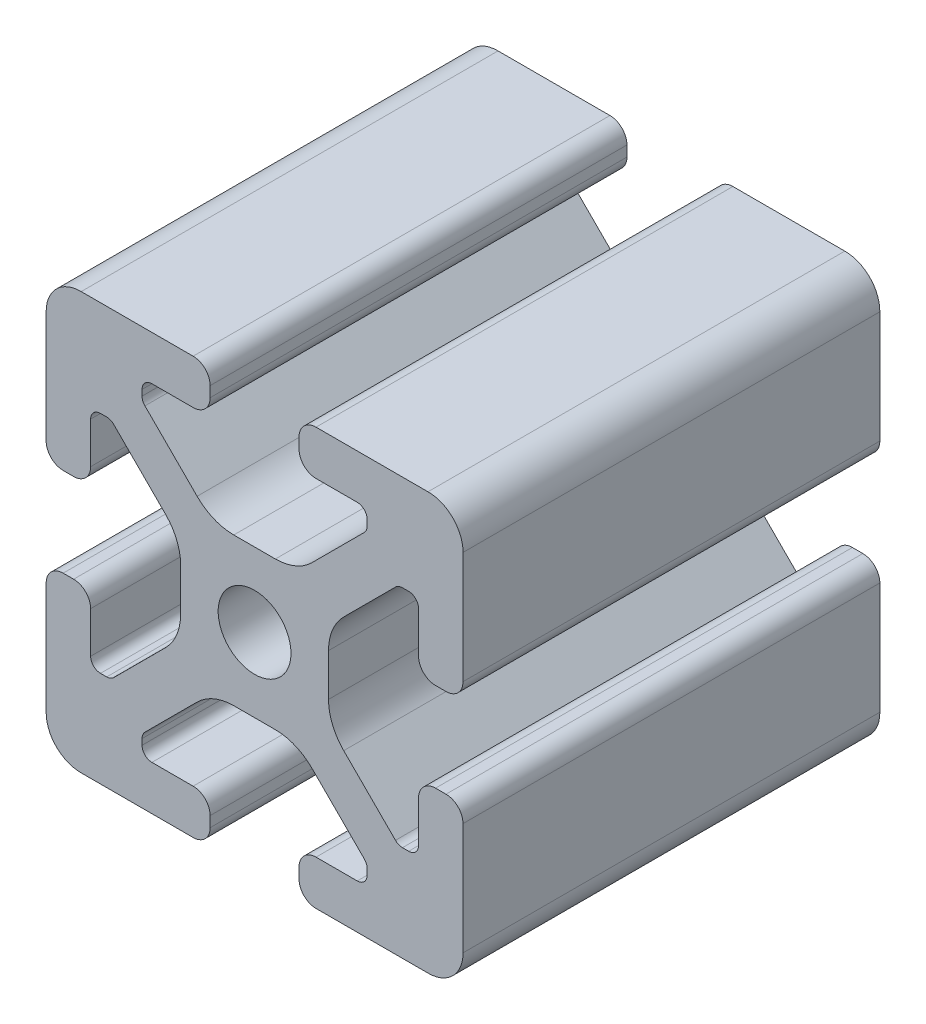
SolidWorks part; units mm, degrees
ref_plane "Front Plane" through (0, 0, 0) normal (0, 0, 1) x (1, 0, 0)
ref_plane "Top Plane" through (0, 0, 0) normal (0, 1, 0) x (1, 0, 0)
ref_plane "Right Plane" through (0, 0, 0) normal (1, 0, 0) x (0, 0, -1)
sketch "Sketch1" plane through (0, 0, 0) normal (0, 0, 1) x (1, 0, 0)
  point P0 (0, 0)
  line B0 (-4.064, 16.5396) -> (-4.064, 17.4964)
  line B1 (-5.6176, 19.05) -> (-15.8475, 19.05)
  line B2 (-19.05, 15.8475) -> (-19.05, 5.6176)
  line B3 (-17.4964, 4.064) -> (-16.5396, 4.064)
  line B4 (-14.986, 5.6176) -> (-14.986, 9.3853)
  line B5 (-14.0843, 10.287) -> (-13.516, 10.287)
  line B6 (-12.8784, 10.0229) -> (-8.1476, 5.2921)
  line B7 (-6.7564, 1.9335) -> (-6.7564, -1.9335)
  line B8 (-8.1476, -5.2921) -> (-12.8784, -10.0229)
  line B9 (-13.516, -10.287) -> (-14.0843, -10.287)
  line B10 (-14.986, -9.3853) -> (-14.986, -5.6176)
  line B11 (-16.5396, -4.064) -> (-17.4964, -4.064)
  line B12 (-19.05, -5.6176) -> (-19.05, -15.8475)
  line B13 (-15.8475, -19.05) -> (-5.6176, -19.05)
  line B14 (-4.064, -17.4964) -> (-4.064, -16.5396)
  line B15 (-5.6176, -14.986) -> (-9.3853, -14.986)
  line B16 (-10.287, -14.0843) -> (-10.287, -13.5524)
  line B17 (-10.0229, -12.9148) -> (-5.2522, -8.144)
  line B18 (-1.9022, -6.7564) -> (1.9022, -6.7564)
  line B19 (5.2522, -8.144) -> (10.0229, -12.9148)
  line B20 (10.287, -13.5524) -> (10.287, -14.0843)
  line B21 (9.3853, -14.986) -> (5.6176, -14.986)
  line B22 (4.064, -16.5396) -> (4.064, -17.4964)
  line B23 (5.6176, -19.05) -> (15.8475, -19.05)
  line B24 (19.05, -15.8475) -> (19.05, -5.6176)
  line B25 (17.4964, -4.064) -> (16.5396, -4.064)
  line B26 (14.986, -5.6176) -> (14.986, -9.3853)
  line B27 (14.0843, -10.287) -> (13.516, -10.287)
  line B28 (12.8784, -10.0229) -> (8.1476, -5.2921)
  line B29 (6.7564, -1.9335) -> (6.7564, 1.9335)
  line B30 (8.1476, 5.2921) -> (12.8784, 10.0229)
  line B31 (13.516, 10.287) -> (14.0843, 10.287)
  line B32 (14.986, 9.3853) -> (14.986, 5.6176)
  line B33 (16.5396, 4.064) -> (17.4964, 4.064)
  line B34 (19.05, 5.6176) -> (19.05, 15.8475)
  line B35 (15.8475, 19.05) -> (5.6176, 19.05)
  line B36 (4.064, 17.4964) -> (4.064, 16.5396)
  line B37 (5.6176, 14.986) -> (9.3853, 14.986)
  line B38 (10.287, 14.0843) -> (10.287, 13.5524)
  line B39 (10.0229, 12.9148) -> (5.2522, 8.144)
  line B40 (1.9022, 6.7564) -> (-1.9022, 6.7564)
  line B41 (-5.2522, 8.144) -> (-10.0229, 12.9148)
  line B42 (-10.287, 13.5524) -> (-10.287, 14.0843)
  line B43 (-9.3853, 14.986) -> (-5.6176, 14.986)
  arc B44 (-5.6176, 14.986) -> (-4.064, 16.5396) centre (-5.6176, 16.5396) ccw
  arc B45 (-4.064, 17.4964) -> (-5.6176, 19.05) centre (-5.6176, 17.4964) ccw
  arc B46 (-15.8475, 19.05) -> (-19.05, 15.8475) centre (-15.8751, 15.8751) ccw
  arc B47 (-19.05, 5.6176) -> (-17.4964, 4.064) centre (-17.4964, 5.6176) ccw
  arc B48 (-16.5396, 4.064) -> (-14.986, 5.6176) centre (-16.5396, 5.6176) ccw
  arc B49 (-14.0843, 10.287) -> (-14.986, 9.3853) centre (-14.0843, 9.3853) ccw
  arc B50 (-12.8784, 10.0229) -> (-13.516, 10.287) centre (-13.516, 9.3853) ccw
  arc B51 (-6.7564, 1.9335) -> (-8.1476, 5.2921) centre (-11.5062, 1.9335) ccw
  arc B52 (-8.1476, -5.2921) -> (-6.7564, -1.9335) centre (-11.5062, -1.9335) ccw
  arc B53 (-13.516, -10.287) -> (-12.8784, -10.0229) centre (-13.516, -9.3853) ccw
  arc B54 (-14.986, -9.3853) -> (-14.0843, -10.287) centre (-14.0843, -9.3853) ccw
  arc B55 (-14.986, -5.6176) -> (-16.5396, -4.064) centre (-16.5396, -5.6176) ccw
  arc B56 (-17.4964, -4.064) -> (-19.05, -5.6176) centre (-17.4964, -5.6176) ccw
  arc B57 (-19.05, -15.8475) -> (-15.8475, -19.05) centre (-15.8751, -15.8751) ccw
  arc B58 (-5.6176, -19.05) -> (-4.064, -17.4964) centre (-5.6176, -17.4964) ccw
  arc B59 (-4.064, -16.5396) -> (-5.6176, -14.986) centre (-5.6176, -16.5396) ccw
  arc B60 (-10.287, -14.0843) -> (-9.3853, -14.986) centre (-9.3853, -14.0843) ccw
  arc B61 (-10.0229, -12.9148) -> (-10.287, -13.5524) centre (-9.3853, -13.5524) ccw
  arc B62 (-1.9022, -6.7564) -> (-5.2522, -8.144) centre (-1.9022, -11.494) ccw
  arc B63 (5.2522, -8.144) -> (1.9022, -6.7564) centre (1.9022, -11.494) ccw
  arc B64 (10.287, -13.5524) -> (10.0229, -12.9148) centre (9.3853, -13.5524) ccw
  arc B65 (9.3853, -14.986) -> (10.287, -14.0843) centre (9.3853, -14.0843) ccw
  arc B66 (5.6176, -14.986) -> (4.064, -16.5396) centre (5.6176, -16.5396) ccw
  arc B67 (4.064, -17.4964) -> (5.6176, -19.05) centre (5.6176, -17.4964) ccw
  arc B68 (15.8475, -19.05) -> (19.05, -15.8475) centre (15.8751, -15.8751) ccw
  arc B69 (19.05, -5.6176) -> (17.4964, -4.064) centre (17.4964, -5.6176) ccw
  arc B70 (16.5396, -4.064) -> (14.986, -5.6176) centre (16.5396, -5.6176) ccw
  arc B71 (14.0843, -10.287) -> (14.986, -9.3853) centre (14.0843, -9.3853) ccw
  arc B72 (12.8784, -10.0229) -> (13.516, -10.287) centre (13.516, -9.3853) ccw
  arc B73 (6.7564, -1.9335) -> (8.1476, -5.2921) centre (11.5062, -1.9335) ccw
  arc B74 (8.1476, 5.2921) -> (6.7564, 1.9335) centre (11.5062, 1.9335) ccw
  arc B75 (13.516, 10.287) -> (12.8784, 10.0229) centre (13.516, 9.3853) ccw
  arc B76 (14.986, 9.3853) -> (14.0843, 10.287) centre (14.0843, 9.3853) ccw
  arc B77 (14.986, 5.6176) -> (16.5396, 4.064) centre (16.5396, 5.6176) ccw
  arc B78 (17.4964, 4.064) -> (19.05, 5.6176) centre (17.4964, 5.6176) ccw
  arc B79 (19.05, 15.8475) -> (15.8475, 19.05) centre (15.8751, 15.8751) ccw
  arc B80 (5.6176, 19.05) -> (4.064, 17.4964) centre (5.6176, 17.4964) ccw
  arc B81 (4.064, 16.5396) -> (5.6176, 14.986) centre (5.6176, 16.5396) ccw
  arc B82 (10.287, 14.0843) -> (9.3853, 14.986) centre (9.3853, 14.0843) ccw
  arc B83 (10.0229, 12.9148) -> (10.287, 13.5524) centre (9.3853, 13.5524) ccw
  arc B84 (1.9022, 6.7564) -> (5.2522, 8.144) centre (1.9022, 11.494) ccw
  arc B85 (-5.2522, 8.144) -> (-1.9022, 6.7564) centre (-1.9022, 11.494) ccw
  arc B86 (-10.287, 13.5524) -> (-10.0229, 12.9148) centre (-9.3853, 13.5524) ccw
  arc B87 (-9.3853, 14.986) -> (-10.287, 14.0843) centre (-9.3853, 14.0843) ccw
  circle B88 centre (0, 0) radius 3.3274
sketch_block_instance "Block-Sketch1-1"
sketch_block "Block-Sketch1"
sketch_block_instance "Block1-2"
sketch_block "Block1"
extrude "Boss-Extrude1" add sketch "Sketch1" along normal mid plane 38.1
